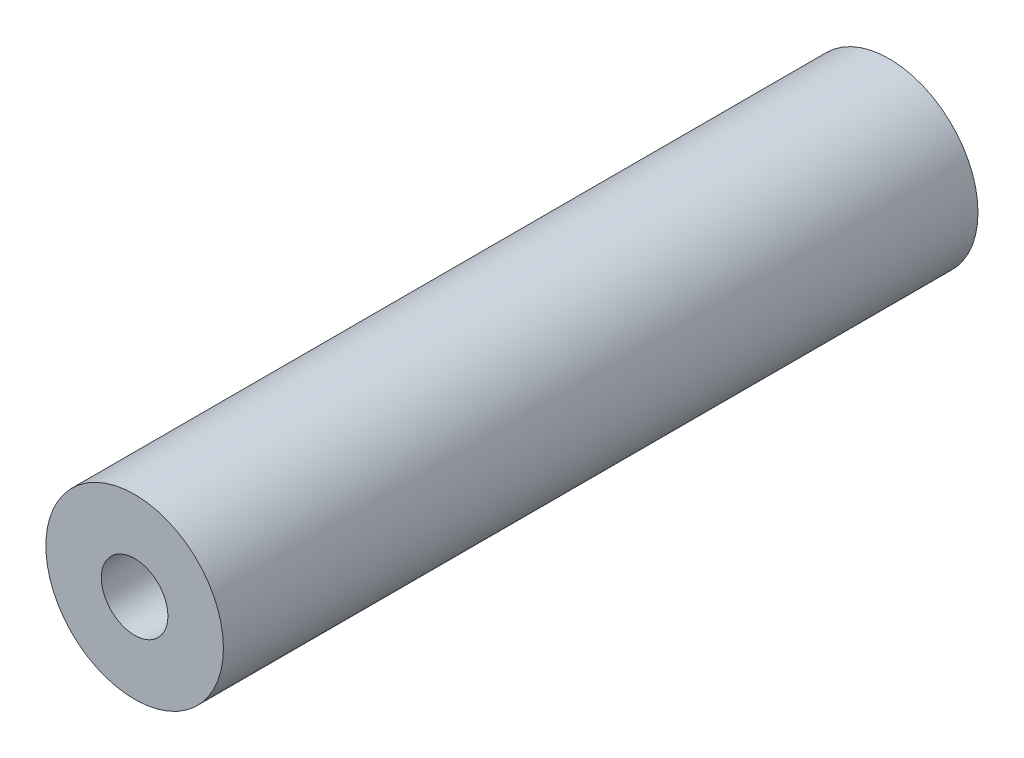
SolidWorks part; units mm, degrees
material "ПТФЭ (общий)"
ref_plane "Спереди" through (0, 0, 0) normal (0, 0, 1) x (1, 0, 0)
ref_plane "Сверху" through (0, 0, 0) normal (0, 1, 0) x (1, 0, 0)
ref_plane "Справа" through (0, 0, 0) normal (1, 0, 0) x (0, 0, -1)
sketch "Эскиз1" plane through (0, 0, 0) normal (0, 0, 1) x (1, 0, 0)
  circle A0 centre (0, 0) radius 4
  circle A1 centre (0, 0) radius 1.5
  dimension "D1" = 3
  dimension "D2" = 8
extrude "Бобышка-Вытянуть1" add sketch "Эскиз1" along normal blind 34
